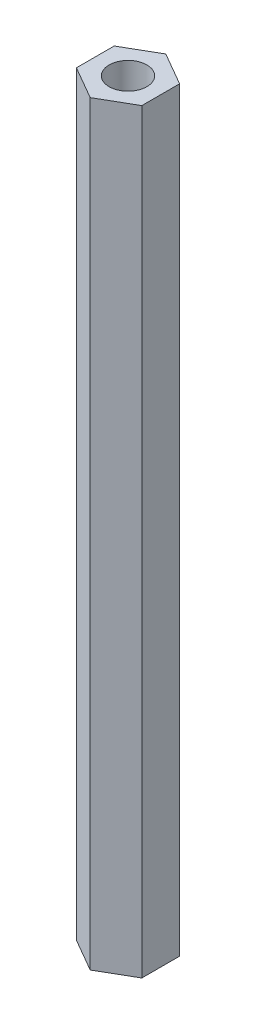
SolidWorks part; units mm, degrees
ref_plane "Face" through (0, 0, 0) normal (0, 0, 1) x (1, 0, 0)
ref_plane "Dessus" through (0, 0, 0) normal (0, 1, 0) x (1, 0, 0)
ref_plane "Droite" through (0, 0, 0) normal (1, 0, 0) x (0, 0, -1)
sketch "Esquisse1" plane through (0, 0, 0) normal (0, 1, 0) x (1, 0, 0)
  line L0 (0, 0) -> (0, 5.5688) construction
  line L1 (0, 5) -> (-4.3301, 2.5)
  line L2 (-4.3301, 2.5) -> (-4.3301, -2.5)
  line L3 (-4.3301, -2.5) -> (0, -5)
  line L4 (0, -5) -> (4.3301, -2.5)
  line L5 (4.3301, -2.5) -> (4.3301, 2.5)
  line L6 (4.3301, 2.5) -> (0, 5)
  circle A0 centre (0, 0) radius 4.3301 construction
  circle A1 centre (0, 0) radius 2.5
  dimension "D1" = 10
  dimension "D2" = 5
extrude "Extrusion1" add sketch "Esquisse1" along normal blind 100
